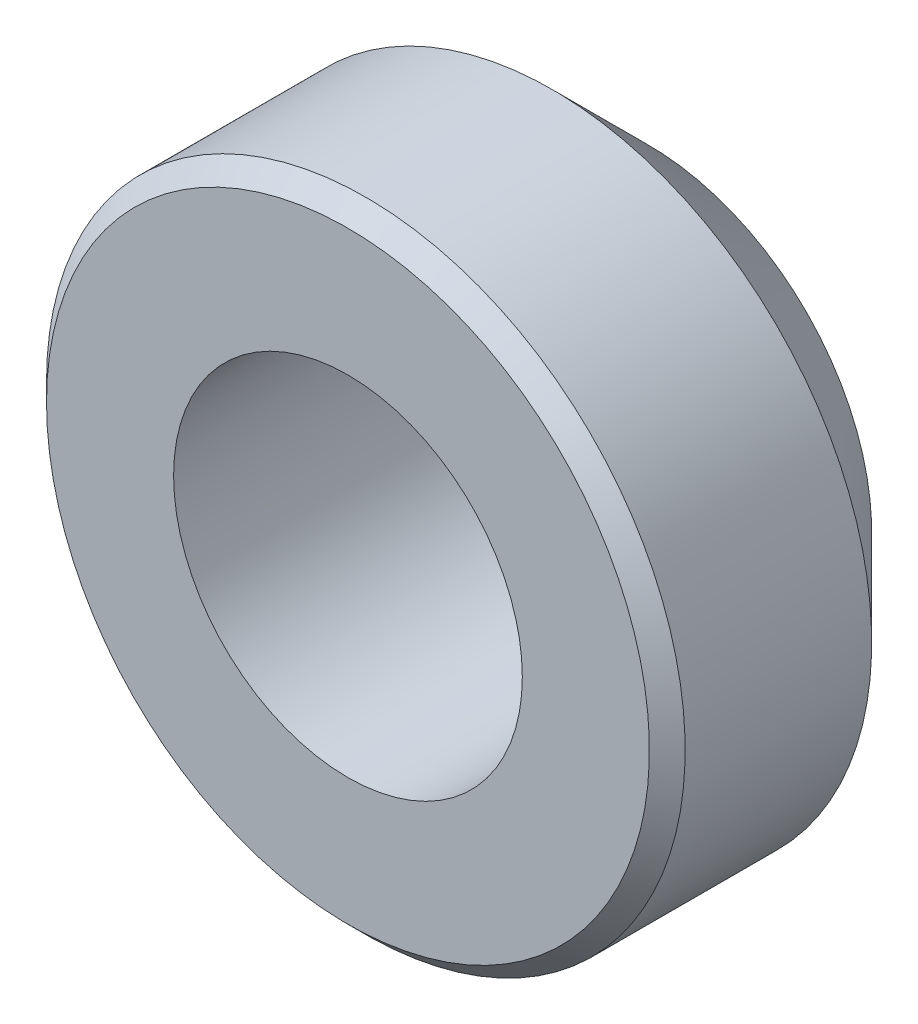
SolidWorks part; units mm, degrees
ref_plane "Front Plane" through (0, 0, 0) normal (0, 0, 1) x (1, 0, 0)
ref_plane "Top Plane" through (0, 0, 0) normal (0, 1, 0) x (1, 0, 0)
ref_plane "Right Plane" through (0, 0, 0) normal (1, 0, 0) x (0, 0, -1)
sketch "Sketch1" plane through (0, 0, 0) normal (0, 1, 0) x (1, 0, 0)
  line L0 (0, 0) -> (0, -6249.7975) construction
  line L1 (0, 0) -> (3.175, 0)
  line L2 (3.175, 0) -> (3.175, 2.032)
  line L3 (3.175, 2.032) -> (2.2225, 2.9845)
  line L4 (2.2225, 2.9845) -> (0, 2.9845)
  line L5 (0, 2.9845) -> (0, 0)
  dimension "D1" = 2.9845
  dimension "D2" = 3.175
  dimension "D3" = 135
  dimension "D4" = 2.032
revolve "Revolve1" add sketch "Sketch1" angle 360 about L0
sketch "Sketch2" plane through (0, 0, -2.9845) normal (0, 0, -1) x (-1, 0, 0)
  circle A0 centre (0, 0) radius 1.7336
  dimension "D1" = 3.4671
extrude "Cut-Extrude1" cut sketch "Sketch2" against normal through all
chamfer "Chamfer1" distance 0.1778 angle 45 1 edges at (-3.175, 0, 0)
